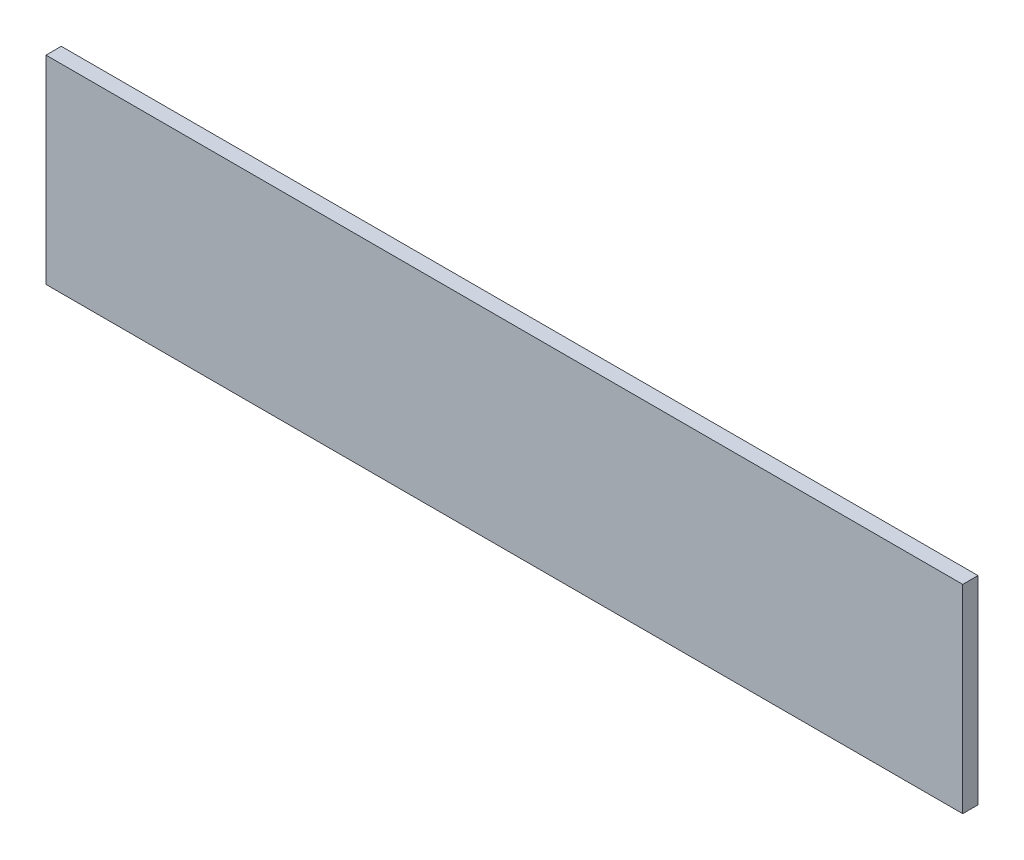
SolidWorks part; units mm, degrees
ref_plane "Plan de face" through (0, 0, 0) normal (0, 0, 1) x (1, 0, 0)
ref_plane "Plan de dessus" through (0, 0, 0) normal (0, 1, 0) x (1, 0, 0)
ref_plane "Plan de droite" through (0, 0, 0) normal (1, 0, 0) x (0, 0, -1)
sketch "Esquisse1" plane through (0, 0, 0) normal (0, 0, 1) x (1, 0, 0)
  line L1 (0, 0) -> (600, 0)
  line L2 (0, 0) -> (0, 130)
  line L3 (0, 130) -> (600, 130)
  line L4 (600, 0) -> (600, 130)
  dimension "D1" = 130
  dimension "D2" = 600
extrude "Boss.-Extru.1" add sketch "Esquisse1" along normal blind 10
